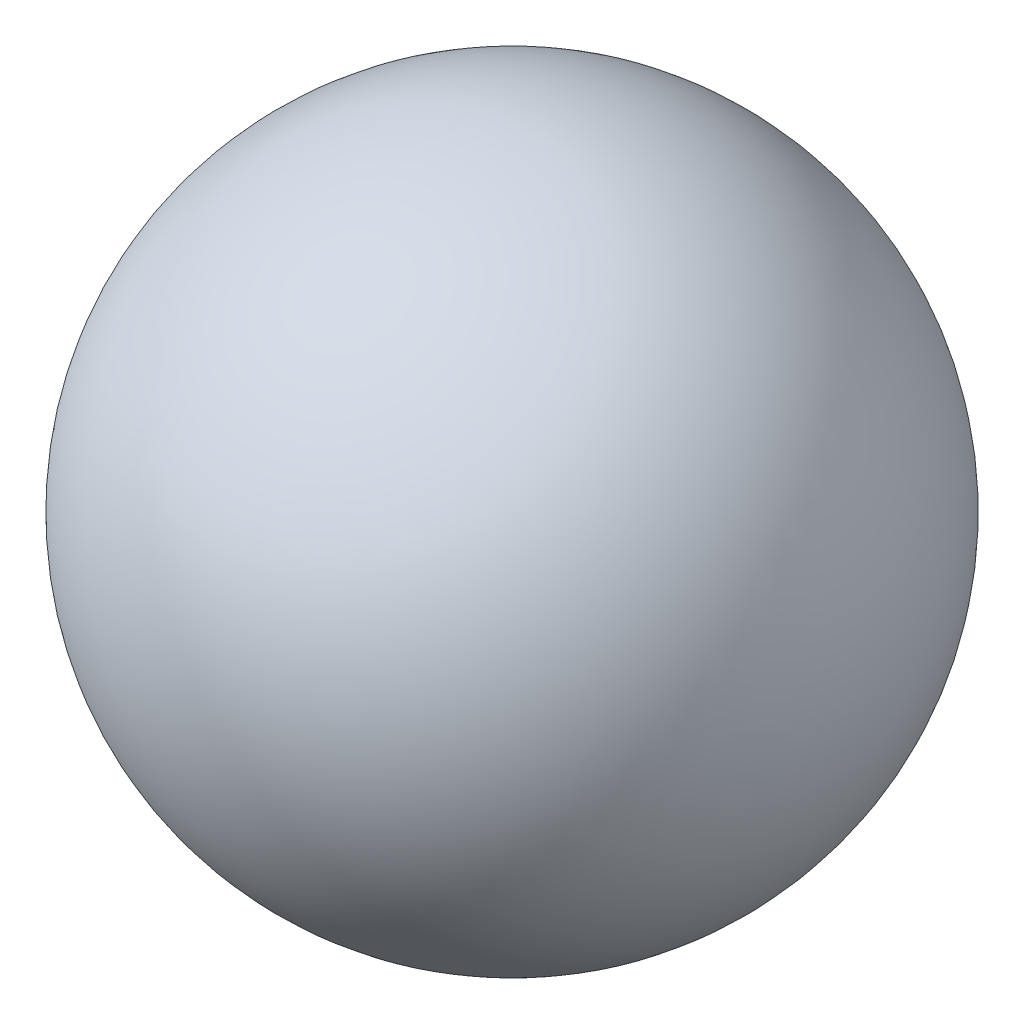
SolidWorks part; units mm, degrees
ref_plane "Plan de face" through (0, 0, 0) normal (0, 0, 1) x (1, 0, 0)
ref_plane "Plan de dessus" through (0, 0, 0) normal (0, 1, 0) x (1, 0, 0)
ref_plane "Plan de droite" through (0, 0, 0) normal (1, 0, 0) x (0, 0, -1)
sketch "Esquisse1" plane through (0, 0, 0) normal (0, 0, 1) x (1, 0, 0)
  line L0 (0, 17.0031) -> (0, -13.9979) construction
  line L1 (0, 2) -> (0, -2)
  arc A0 (0, 2) -> (0, -2) centre (0, 0) cw
  dimension "D1" = 2
revolve "Révolution1" add sketch "Esquisse1" angle 360 about L0
